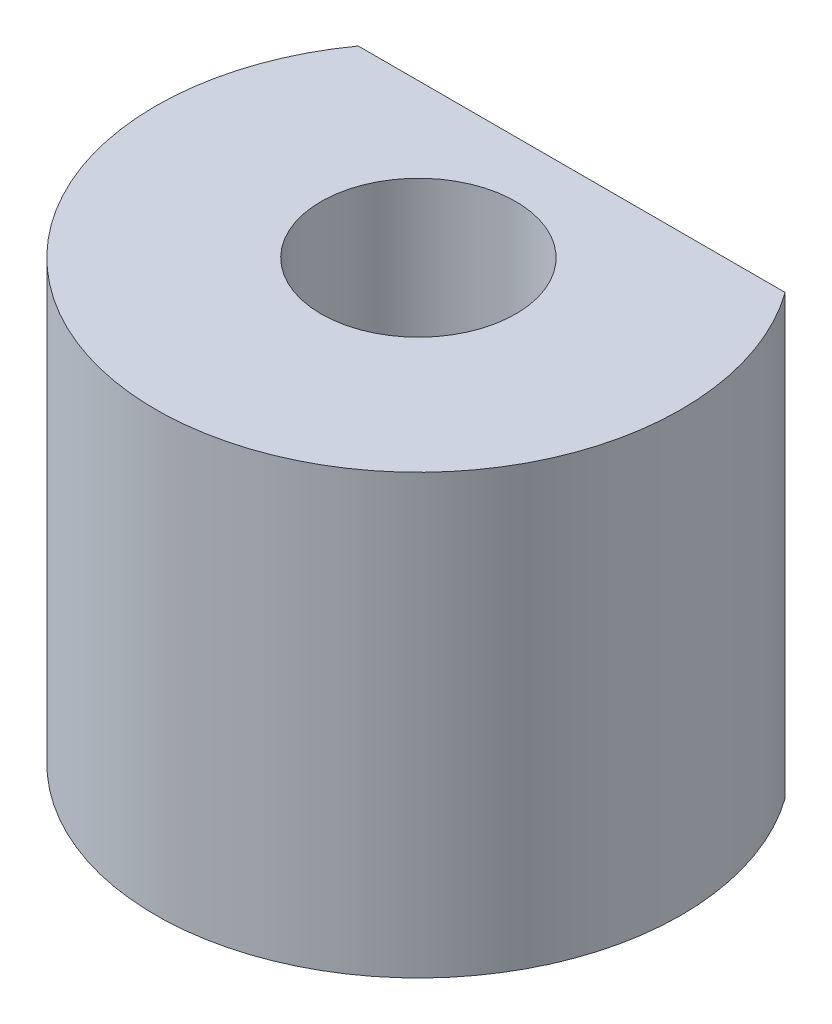
SolidWorks part; units mm, degrees
material "ABS"
ref_plane "Front Plane" through (0, 0, 0) normal (0, 0, 1) x (1, 0, 0)
ref_plane "Top Plane" through (0, 0, 0) normal (0, 1, 0) x (1, 0, 0)
ref_plane "Right Plane" through (0, 0, 0) normal (1, 0, 0) x (0, 0, -1)
sketch "Sketch1" plane through (0, 0, 0) normal (0, 1, 0) x (1, 0, 0)
  line L0 (-6, 0) -> (6, 0) construction
  line L5 (-4.8734, 3.5) -> (4.8734, 3.5)
  circle A0 centre (0, 0) radius 2.2238
  circle A1 centre (0, 0) radius 6
  circle A2 centre (-0.8, -0.4619) radius 0.8
  circle A3 centre (0, 0.9238) radius 0.8
  circle A4 centre (0.8, -0.4619) radius 0.8
  circle A5 centre (0, 0) radius 1.7238
  dimension "D1" = 12
  dimension "D2" = 1.6
  dimension "D3" = 0.5
  dimension "D4" = 3.5
extrude "Boss-Extrude1" add sketch "Sketch1" along normal blind 10
